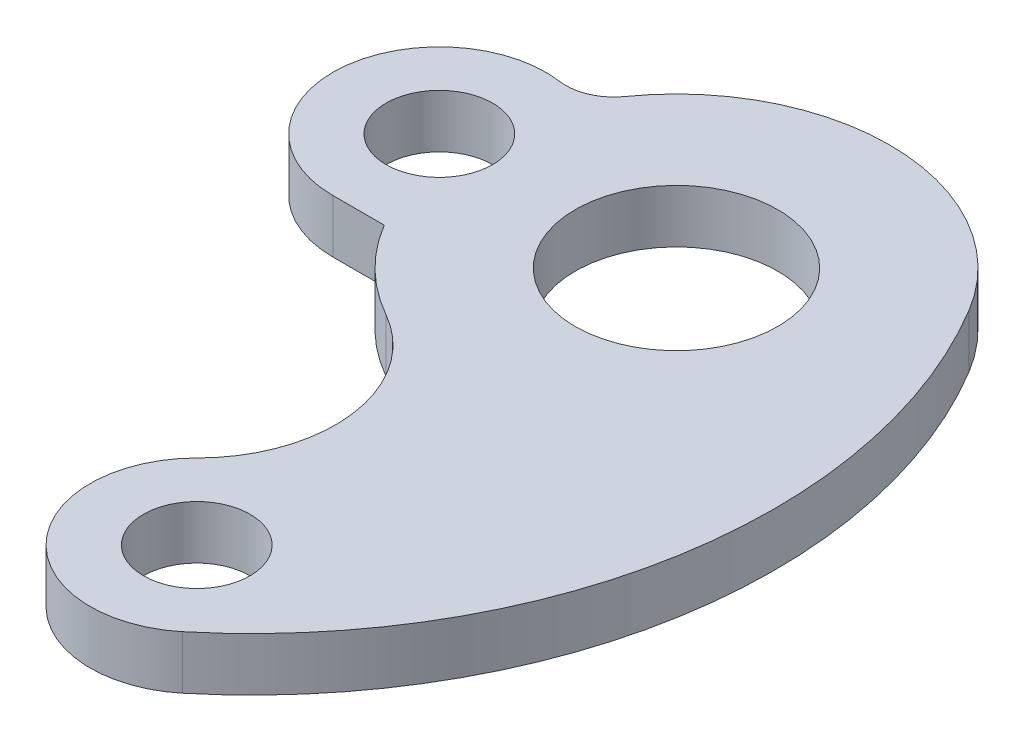
SolidWorks part; units mm, degrees
ref_plane "Front Plane" through (0, 0, 0) normal (0, 0, 1) x (1, 0, 0)
ref_plane "Top Plane" through (0, 0, 0) normal (0, 1, 0) x (1, 0, 0)
ref_plane "Right Plane" through (0, 0, 0) normal (1, 0, 0) x (0, 0, -1)
sketch "Sketch7" plane through (0, 0, 0) normal (0, 1, 0) x (1, 0, 0)
  line L0 (0, 0) -> (0, 40) construction
  line L1 (0, 40) -> (0, -19) construction
  line L2 (43.6252, 0) -> (40, 0) construction
  line L3 (-45, 19.5346) -> (-45, 0) construction
  line L4 (-20, -90) -> (10, -90) construction
  line L5 (-44.0445, -20.4425) -> (-34.3817, -20.4425)
  line L6 (0, -80) -> (0, -102.5515) construction
  line L7 (19, 0) -> (-19, 0) construction
  line L8 (20, -90) -> (27.6936, -90) construction
  circle A0 centre (0, 0) radius 14
  circle A1 centre (0, 0) radius 19
  arc A2 (-34.3817, -20.4425) -> (-19.6959, -34.8148) centre (0, 0) ccw
  arc A3 (-41.2676, 19.3637) -> (-44.0445, -20.4425) centre (-44.0445, -0.4425) ccw
  arc A4 (-14.1297, -75.8454) -> (12.745, -105.4131) centre (0, -90) ccw
  circle A5 centre (0, -90) radius 10
  arc A6 (12.745, -105.4131) -> (34.2798, 20.613) centre (-49.7057, -29.8889) ccw
  arc A7 (-14.1297, -75.8454) -> (-19.6959, -34.8148) centre (-32.4982, -57.4444) ccw
  arc A8 (-41.2676, 19.3637) -> (-32.6677, 23.0829) centre (-40.0179, 28.2766) ccw
  arc A9 (34.2798, 20.613) -> (-32.6677, 23.0829) centre (0, 0) ccw
  circle A10 centre (-44.0445, -0.4425) radius 10
  dimension "D3" = 28
  dimension "D4" = 38
  dimension "D5" = 80
  dimension "D6" = 40
  dimension "D7" = 20
  dimension "D8" = 196
  dimension "D9" = 52
  dimension "D10" = 9
  dimension "D1" = 90
  dimension "D2" = 45
extrude "Boss-Extrude7" add sketch "Sketch7" along normal blind 10 contours A6 A9 A8 A3 L5 A2 A7 A4 A10 A1 A5
